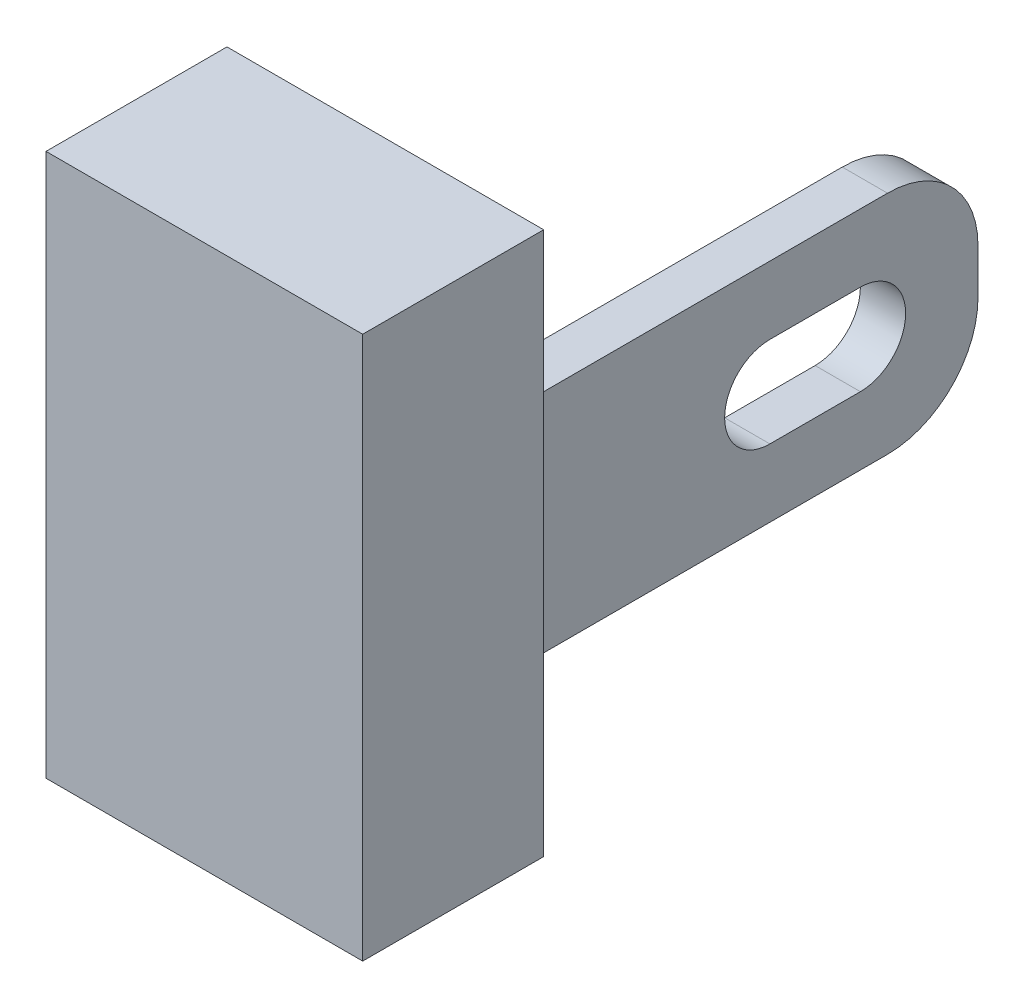
SolidWorks part; units mm, degrees
ref_plane "Front Plane" through (0, 0, 0) normal (0, 0, 1) x (1, 0, 0)
ref_plane "Top Plane" through (0, 0, 0) normal (0, 1, 0) x (1, 0, 0)
ref_plane "Right Plane" through (0, 0, 0) normal (1, 0, 0) x (0, 0, -1)
sketch "Sketch1" plane through (0, 0, 0) normal (0, 0, 1) x (1, 0, 0)
  line L1 (1.75, -3) -> (-1.75, -3)
  line L2 (1.75, -3) -> (1.75, 3)
  line L3 (1.75, 3) -> (-1.75, 3)
  line L4 (-1.75, -3) -> (-1.75, 3)
  line L5 (1.75, -3) -> (-1.75, 3) construction
  line L6 (1.75, 3) -> (-1.75, -3) construction
  point P0 (0, 0)
  dimension "D1" = 6
  dimension "D2" = 3.5
extrude "Boss-Extrude1" add sketch "Sketch1" along normal blind 2
sketch "Sketch2" plane through (0, 0, 0) normal (0, 0, -1) x (-1, 0, 0)
  line L0 (-1.75, -3) -> (-1.75, 3) construction
  line L1 (-1.55, -1.25) -> (-1.05, -1.25)
  line L2 (-1.55, -1.25) -> (-1.55, 1.25)
  line L3 (-1.55, 1.25) -> (-1.05, 1.25)
  line L4 (-1.05, -1.25) -> (-1.05, 1.25)
  line L5 (-1.55, -1.25) -> (-1.05, 1.25) construction
  line L6 (-1.55, 1.25) -> (-1.05, -1.25) construction
  point P0 (-1.3, 0)
  dimension "D1" = 0.2
  dimension "D2" = 0.5
  dimension "D3" = 2.5
extrude "Boss-Extrude2" add sketch "Sketch2" along normal blind 5
fillet "Fillet1" radius 1 2 edges at (1.3, -1.25, -5) (1.3, 1.25, -5)
sketch "Sketch3" plane through (1.55, 0, 0) normal (1, 0, 0) x (0, 0, -1)
  line L0 (2.7, 0) -> (3.7, 0) construction
  line L1 (2.7, 0.5) -> (3.7, 0.5)
  line L2 (2.7, -0.5) -> (3.7, -0.5)
  line L3 (5, 0.25) -> (5, -0.25) construction
  arc A0 (2.7, 0.5) -> (2.7, -0.5) centre (2.7, 0) ccw
  arc A1 (3.7, -0.5) -> (3.7, 0.5) centre (3.7, 0) ccw
  point P3 (3.2, 0)
  dimension "D1" = 0.5
  dimension "D3" = 1.3
  dimension "D2" = 1
extrude "Cut-Extrude1" cut sketch "Sketch3" against normal blind 5
